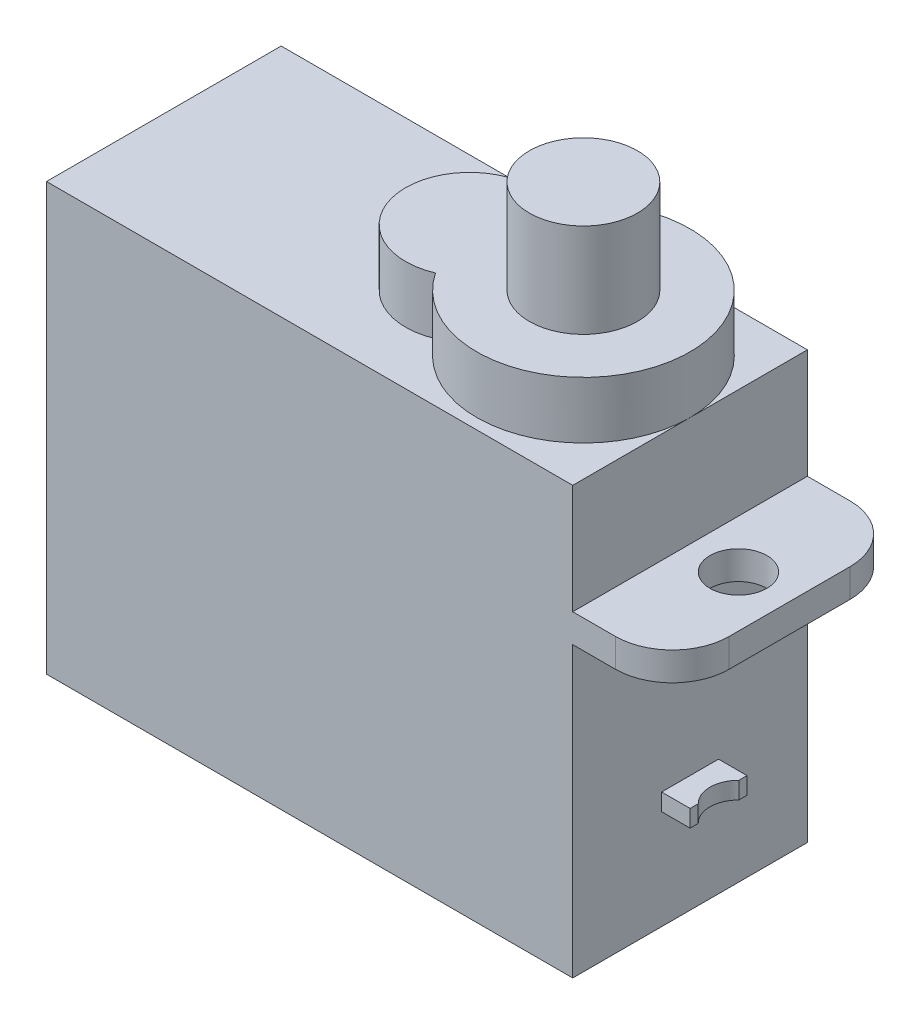
SolidWorks part; units mm, degrees
ref_plane "Front" through (0, 0, 0) normal (0, 0, 1) x (1, 0, 0)
ref_plane "Top" through (0, 0, 0) normal (0, 1, 0) x (1, 0, 0)
ref_plane "Right" through (0, 0, 0) normal (1, 0, 0) x (0, 0, -1)
sketch "草图1" plane through (0, 0, 0) normal (0, 1, 0) x (1, 0, 0)
  line L1 (9.25, -4.125) -> (-9.25, -4.125)
  line L2 (9.25, -4.125) -> (9.25, 4.125)
  line L3 (9.25, 4.125) -> (-9.25, 4.125)
  line L4 (-9.25, -4.125) -> (-9.25, 4.125)
  line L5 (9.25, -4.125) -> (-9.25, 4.125) construction
  line L6 (9.25, 4.125) -> (-9.25, -4.125) construction
  point P0 (0, 0)
  dimension "D1" = 18.5
  dimension "D2" = 8.25
extrude "凸台-拉伸1" add sketch "草图1" along normal blind 15
sketch "草图2" plane through (0, 15, 0) normal (0, 1, 0) x (1, 0, 0)
  line L0 (-14.8322, 0) -> (13.7625, 0) construction
  line L1 (9.25, -4.125) -> (9.25, 4.125) construction
  circle A0 centre (5.5, 0) radius 3.75
  dimension "D2" = 7.5
  dimension "D1" = 3.75
extrude "凸台-拉伸2" add sketch "草图2" along normal blind 2
sketch "草图3" plane through (0, 15, 0) normal (0, 1, 0) x (1, 0, 0)
  line L0 (-11.0431, 0) -> (11.1033, 0) construction
  circle A0 centre (1.5, 0) radius 2.25
  circle A1 centre (5.5, 0) radius 3.75 construction
  dimension "D2" = 4.5
  dimension "D1" = 4
extrude "凸台-拉伸3" add sketch "草图3" along normal blind 2
sketch "草图4" plane through (0, 17, 0) normal (0, 1, 0) x (1, 0, 0)
  circle A0 centre (5.5, 0) radius 1.9
  dimension "D1" = 3.8
extrude "凸台-拉伸4" add sketch "草图4" along normal blind 3.3
sketch "草图5" plane through (9.25, 0, 0) normal (1, 0, 0) x (0, 0, -1)
  line L0 (0, -4.1819) -> (0, 9.9009) construction
  line L1 (-4.125, 0) -> (4.125, 0) construction
  line L2 (1, 3.5) -> (-1, 3.5)
  line L3 (1, 3.5) -> (1, 4.1)
  line L4 (1, 4.1) -> (-1, 4.1)
  line L5 (-1, 3.5) -> (-1, 4.1)
  line L6 (1, 3.5) -> (-1, 4.1) construction
  line L7 (1, 4.1) -> (-1, 3.5) construction
  point P3 (0, 3.8)
  dimension "D1" = 0.6
  dimension "D2" = 2
  dimension "D3" = 3.8
extrude "凸台-拉伸5" add sketch "草图5" along normal blind 1
ref_plane "基准面1" through (0, 10.15, 0) normal (0, 1, 0) x (1, 0, 0)
sketch "草图6" plane through (0, 10.15, 0) normal (0, 1, 0) x (1, 0, 0)
  line L0 (9.25, 4.125) -> (-9.25, 4.125) construction
  line L1 (12.75, -4.125) -> (-12.75, -4.125)
  line L2 (12.75, -4.125) -> (12.75, 4.125)
  line L3 (12.75, 4.125) -> (-12.75, 4.125)
  line L4 (-12.75, -4.125) -> (-12.75, 4.125)
  line L5 (12.75, -4.125) -> (-12.75, 4.125) construction
  line L6 (12.75, 4.125) -> (-12.75, -4.125) construction
  point P0 (0, 0)
  dimension "D1" = 25.5
extrude "凸台-拉伸6" add sketch "草图6" along normal blind 1
sketch "草图7" plane through (0, 11.15, 0) normal (0, 1, 0) x (1, 0, 0)
  line L0 (-27.0033, 0) -> (51.0137, 0) construction
  line L1 (0, 18.5656) -> (0, -16.9191) construction
  circle A0 centre (-10.95, 0) radius 1
  circle A1 centre (10.95, 0) radius 1
  dimension "D2" = 2
  dimension "D1" = 21.9
extrude "切除-拉伸1" cut sketch "草图7" against normal through all
fillet "圆角1" radius 2 4 edges at (12.75, 10.65, -4.125) (12.75, 10.65, 4.125) (-12.75, 10.65, -4.125) (-12.75, 10.65, 4.125)
sketch "草图8" plane through (0, 11.15, 0) normal (0, 1, 0) x (1, 0, 0)
  line L1 (-9.25, -4.125) -> (-15.0575, -4.125)
  line L2 (-9.25, -4.125) -> (-9.25, 4.9738)
  line L3 (-9.25, 4.9738) -> (-15.0575, 4.9738)
  line L4 (-15.0575, -4.125) -> (-15.0575, 4.9738)
extrude "切除-拉伸2" cut sketch "草图8" against normal blind 2
